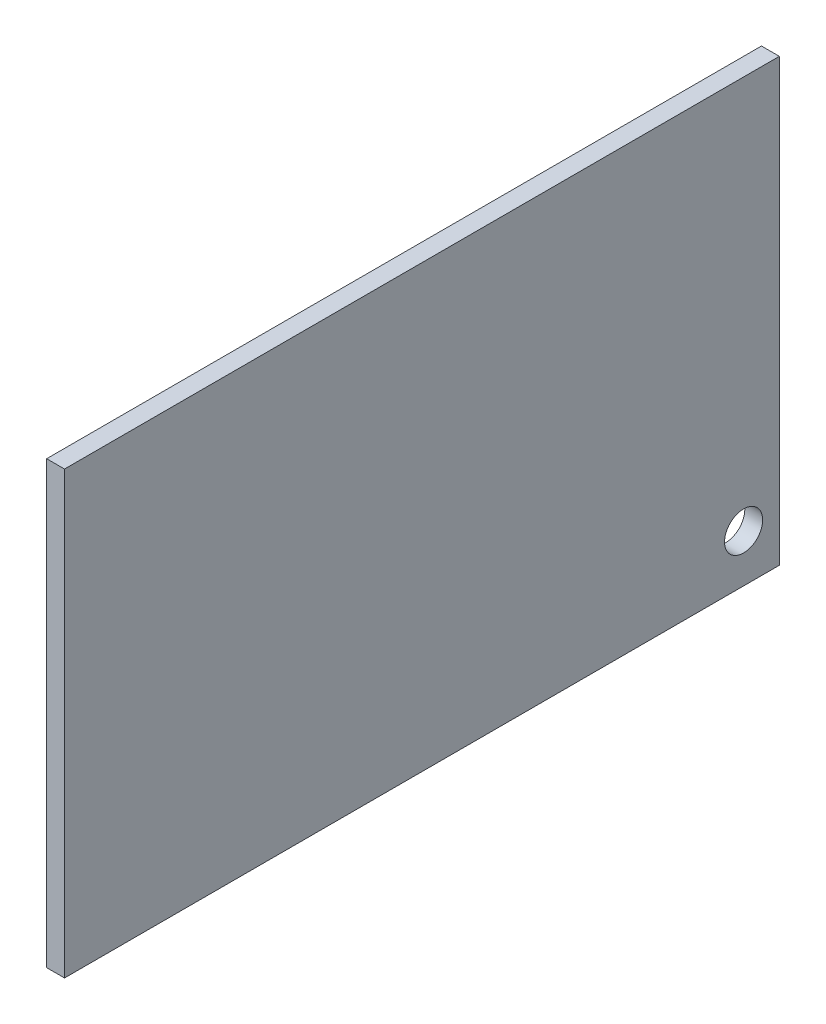
SolidWorks part; units mm, degrees
ref_plane "Спереди" through (0, 0, 0) normal (0, 0, 1) x (1, 0, 0)
ref_plane "Сверху" through (0, 0, 0) normal (0, 1, 0) x (1, 0, 0)
ref_plane "Справа" through (0, 0, 0) normal (1, 0, 0) x (0, 0, -1)
sketch "Эскиз1" plane through (0, 0, 0) normal (1, 0, 0) x (0, 0, -1)
  line L1 (0, 0) -> (60, 0)
  line L2 (0, 0) -> (0, 37)
  line L3 (0, 37) -> (60, 37)
  line L4 (60, 0) -> (60, 37)
  circle A0 centre (3, 34) radius 1.6
  circle A1 centre (57, 34) radius 1.6
  circle A2 centre (57, 4) radius 1.6
  circle A3 centre (3, 4) radius 1.6
  dimension "D3" = 3.2
  dimension "D4" = 4
  dimension "D5" = 3
  dimension "D6" = 3
  dimension "D7" = 3
  dimension "D1" = 37
  dimension "D2" = 60
extrude "Бобышка-Вытянуть1" add sketch "Эскиз1" along normal blind 1.5 contours L1 L4 L3 L2 A3 A2 A1 A0 | A0 | A3 | A1
